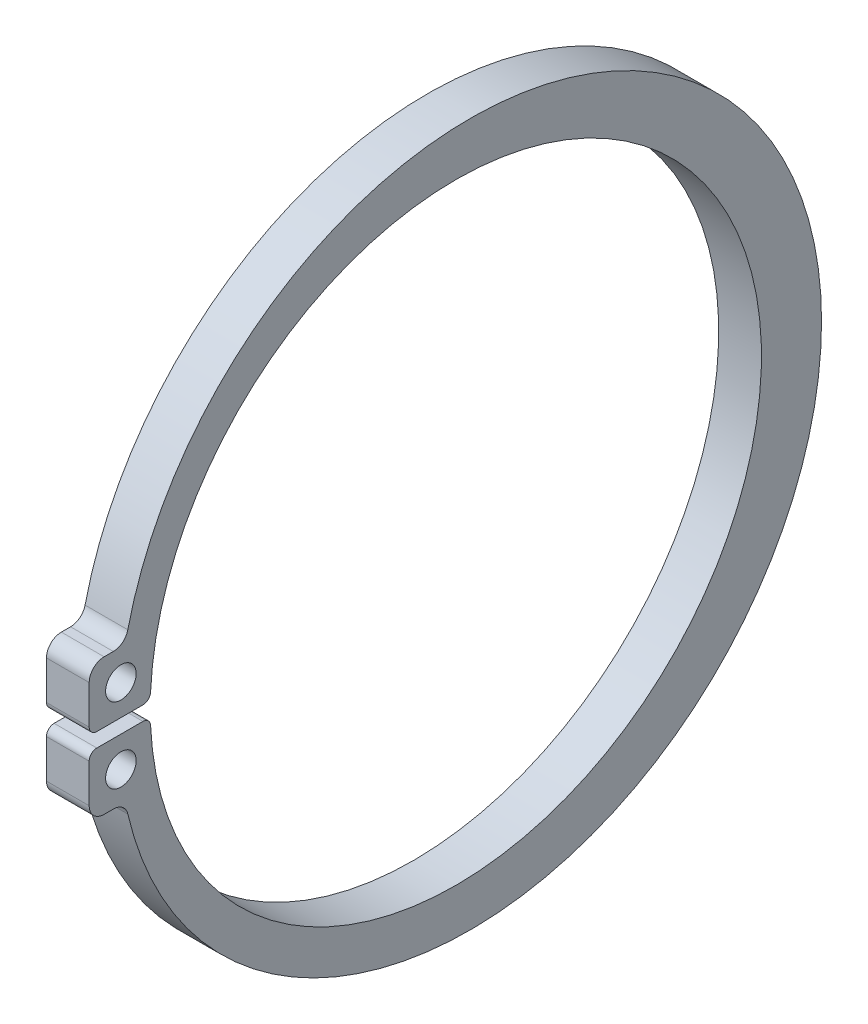
SolidWorks part; units mm, degrees
ref_plane "Спереди" through (0, 0, 0) normal (0, 0, 1) x (1, 0, 0)
ref_plane "Сверху" through (0, 0, 0) normal (0, 1, 0) x (1, 0, 0)
ref_plane "Справа" through (0, 0, 0) normal (1, 0, 0) x (0, 0, -1)
ref_plane "Плоскость4" through (-34, 0, 0) normal (-1, 0, 0) x (0, -1, 0)
sketch "Эскиз1" plane through (-34, 0, 0) normal (-1, 0, 0) x (0, -1, 0)
  line L0 (-8.3892, -1.2575) -> (-8.3892, -0.1787)
  line L1 (-8.5679, 0) -> (-9.4704, 0)
  line L2 (-9.8192, -0.3488) -> (-9.8192, -0.5638)
  line L3 (-6.6258, -0.5638) -> (-6.6258, -0.3488)
  line L4 (-6.9746, 0) -> (-7.8771, 0)
  line L5 (-8.0558, -0.1787) -> (-8.0558, -1.2575)
  circle A0 centre (-9.1042, -0.7413) radius 0.3575
  circle A1 centre (-7.3408, -0.7413) radius 0.3575
  arc A2 (-8.3892, -0.1787) -> (-8.5679, 0) centre (-8.5679, -0.1787) ccw
  arc A3 (-9.4704, 0) -> (-9.8192, -0.3488) centre (-9.4704, -0.3488) ccw
  arc A4 (-9.8192, -0.5638) -> (-10.0888, -0.9035) centre (-10.1679, -0.5638) cw
  arc A5 (-10.0888, -0.9035) -> (-6.3562, -0.9035) centre (-8.2225, -8.9114) ccw
  arc A6 (-6.3562, -0.9035) -> (-6.6258, -0.5638) centre (-6.2771, -0.5638) cw
  arc A7 (-6.6258, -0.3488) -> (-6.9746, 0) centre (-6.9746, -0.3488) ccw
  arc A8 (-7.8771, 0) -> (-8.0558, -0.1787) centre (-7.8771, -0.1787) ccw
  arc A9 (-8.0558, -1.2575) -> (-7.8855, -1.436) centre (-7.8771, -1.2575) ccw
  arc A10 (-7.8855, -1.436) -> (-8.5595, -1.436) centre (-8.2225, -8.5781) cw
  arc A11 (-8.5595, -1.436) -> (-8.3892, -1.2575) centre (-8.5679, -1.2575) ccw
extrude "Бобышка-Вытянуть1" add sketch "Эскиз1" against normal blind 1
